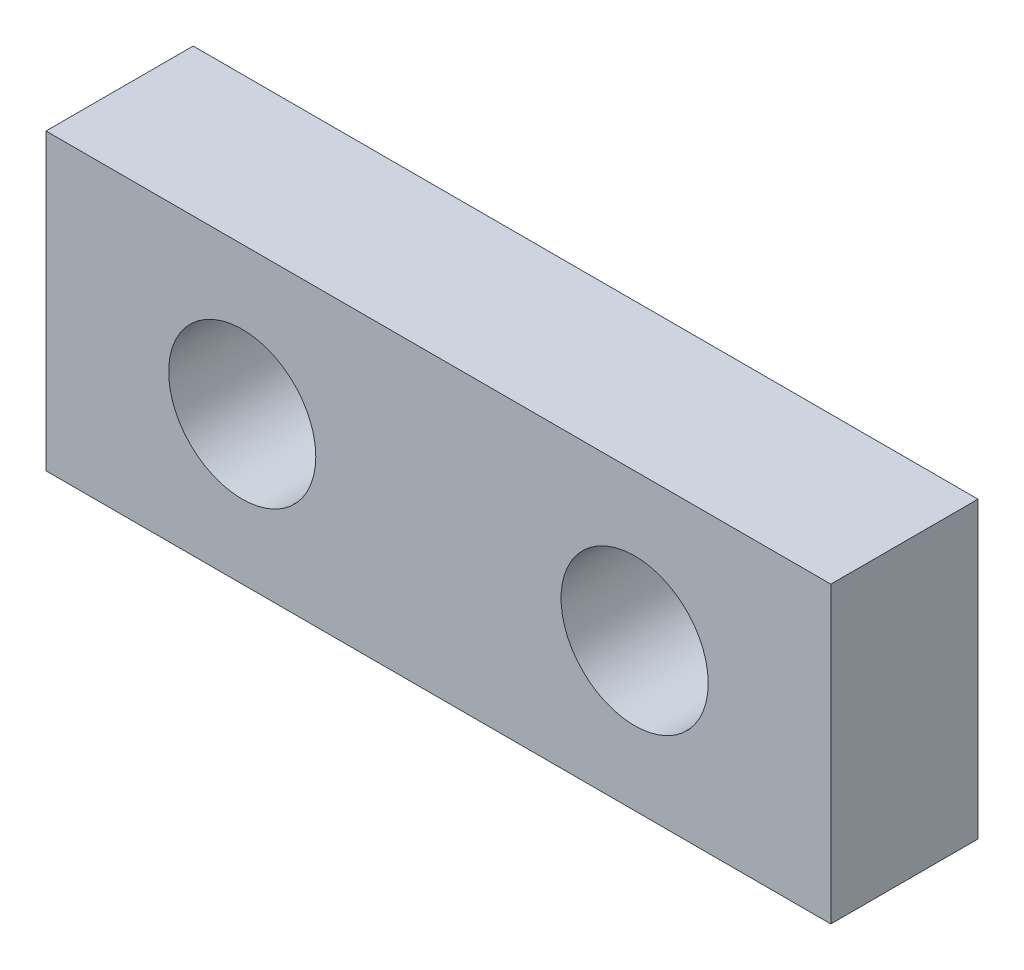
SolidWorks part; units mm, degrees
ref_plane "正面" through (0, 0, 0) normal (0, 0, 1) x (1, 0, 0)
ref_plane "平面" through (0, 0, 0) normal (0, 1, 0) x (1, 0, 0)
ref_plane "右側面" through (0, 0, 0) normal (1, 0, 0) x (0, 0, -1)
sketch "ｽｹｯﾁ1" plane through (0, 0, 0) normal (0, 0, 1) x (1, 0, 0)
  line L1 (-8, 3) -> (8, 3)
  line L2 (-8, 3) -> (-8, -3)
  line L3 (-8, -3) -> (8, -3)
  line L4 (8, 3) -> (8, -3)
  line L5 (-8, 3) -> (8, -3) construction
  line L6 (-8, -3) -> (8, 3) construction
  point P0 (0, 0)
  dimension "D1" = 6
  dimension "D2" = 16
extrude "ﾎﾞｽ - 押し出し1" add sketch "ｽｹｯﾁ1" along normal blind 3
sketch "ｽｹｯﾁ2" plane through (0, 0, 3) normal (0, 0, 1) x (1, 0, 0)
  line L0 (-8, 0) -> (-4, 0)
  line L1 (-8, 3) -> (-8, -3) construction
  line L2 (-4, 0) -> (4, 0)
  circle A0 centre (-4, 0) radius 1.5
  circle A1 centre (4, 0) radius 1.5
  dimension "D2" = 3
  dimension "D4" = 3
  dimension "D1" = 4
  dimension "D3" = 8
extrude "ｶｯﾄ - 押し出し1" cut sketch "ｽｹｯﾁ2" against normal blind 3
